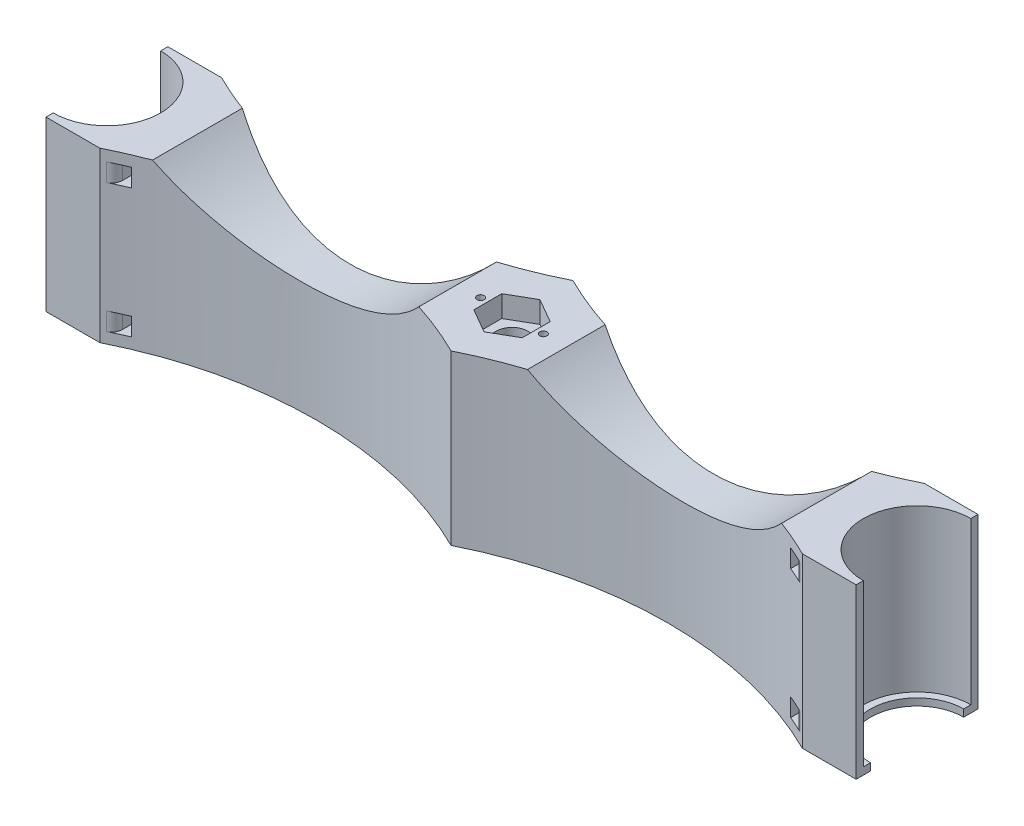
SolidWorks part; units mm, degrees
material "Copper"
ref_plane "Front Plane" through (0, 0, 0) normal (0, 0, 1) x (1, 0, 0)
ref_plane "Top Plane" through (0, 0, 0) normal (0, 1, 0) x (1, 0, 0)
ref_plane "Right Plane" through (0, 0, 0) normal (1, 0, 0) x (0, 0, -1)
sketch "Sketch1" plane through (0, 0, 0) normal (0, 1, 0) x (1, 0, 0)
  line L0 (0, 15) -> (0, 17)
  line L1 (0, -15) -> (0, -17)
  line L2 (113, 96.8217) -> (113, -79.4167) construction
  line L3 (0, 17) -> (15, 17)
  line L4 (226, -17) -> (211, -17)
  line L5 (226, 17) -> (211, 17)
  line L6 (0, -17) -> (15, -17)
  line L7 (226, -15) -> (226, -17)
  line L8 (226, 15) -> (226, 17)
  arc A0 (0, -15) -> (0, 15) centre (0, 0) ccw
  arc A1 (15, 17) -> (113, 17) centre (64, 115.4835) ccw
  arc A2 (15, -17) -> (113, -17) centre (64, -115.4835) cw
  arc A3 (211, -17) -> (113, -17) centre (162, -115.4835) ccw
  arc A4 (211, 17) -> (113, 17) centre (162, 115.4835) cw
  arc A5 (226, -15) -> (226, 15) centre (226, 0) cw
  dimension "D1" = 113
extrude "Boss-Extrude2" add sketch "Sketch1" along normal blind 47
sketch "Sketch2" plane through (0, 47, 0) normal (0, 1, 0) x (1, 0, 0)
  circle A0 centre (113, 0) radius 4.5
extrude "Cut-Extrude1" cut sketch "Sketch2" against normal through all
sketch "Sketch3" plane through (0, 47, 0) normal (0, 1, 0) x (1, 0, 0)
  line L1 (113, -7.7942) -> (119.75, -3.8971)
  line L2 (119.75, -3.8971) -> (119.75, 3.8971)
  line L3 (119.75, 3.8971) -> (113, 7.7942)
  line L4 (113, 7.7942) -> (106.25, 3.8971)
  line L5 (106.25, 3.8971) -> (106.25, -3.8971)
  line L6 (106.25, -3.8971) -> (113, -7.7942)
  circle A0 centre (113, 0) radius 6.75 construction
extrude "Cut-Extrude2" cut sketch "Sketch3" against normal blind 6
sketch "Sketch4" plane through (0, 47, 0) normal (0, 1, 0) x (1, 0, 0)
  line L0 (106.25, 3.8971) -> (106.25, -3.8971) construction
  line L1 (119.75, -3.8971) -> (119.75, 3.8971) construction
  circle A0 centre (104.25, 0) radius 1
  circle A1 centre (121.75, 0) radius 1
  dimension "D1" = 2
  dimension "D2" = 2
extrude "Cut-Extrude3" cut sketch "Sketch4" against normal blind 6
ref_plane "Plane1" through (0, 0, -17) normal (0, 0, -1) x (-1, 0, 0)
sketch "Sketch5" plane through (0, 0, -17) normal (0, 0, -1) x (-1, 0, 0)
  line L0 (-15, 47) -> (-113, 47) construction
  line L1 (-113, 47) -> (-113, 0) construction
  line L2 (-200.7496, 47) -> (-128.1535, 47)
  line L3 (-97.8465, 47) -> (-25.2504, 47)
  line L4 (-25.2504, 47) -> (-24.7481, 45.6215)
  arc A0 (-25.2504, 47) -> (-97.8465, 47) centre (-61.5485, 81.298) cw
  arc A1 (-200.7496, 47) -> (-128.1535, 47) centre (-164.4515, 81.298) ccw
extrude "Cut-Extrude4" cut sketch "Sketch5" against normal through all contours L2 A1 | A0 L3
sketch "Sketch6" plane through (0, 0, 0) normal (0, -1, 0) x (1, 0, 0)
  line L1 (120.5056, 0) -> (116.7528, 6.5)
  line L2 (116.7528, 6.5) -> (109.2472, 6.5)
  line L3 (109.2472, 6.5) -> (105.4944, 0)
  line L4 (105.4944, 0) -> (109.2472, -6.5)
  line L5 (109.2472, -6.5) -> (116.7528, -6.5)
  line L6 (116.7528, -6.5) -> (120.5056, 0)
  circle A0 centre (113, 0) radius 6.5 construction
extrude "Cut-Extrude5" cut sketch "Sketch6" against normal blind 6
sketch "Sketch7" plane through (0, 6, 0) normal (0, -1, 0) x (1, 0, 0)
  line L1 (120.5056, 0) -> (116.7528, 6.5)
  line L2 (116.7528, 6.5) -> (109.2472, 6.5)
  line L3 (109.2472, 6.5) -> (105.4944, 0)
  line L4 (105.4944, 0) -> (109.2472, -6.5)
  line L5 (109.2472, -6.5) -> (116.7528, -6.5)
  line L6 (116.7528, -6.5) -> (120.5056, 0)
  circle A0 centre (113, 0) radius 6.5 construction
extrude "Boss-Extrude3" add sketch "Sketch7" along normal blind 0.2
sketch "Sketch10" plane through (0, 0, 0) normal (0, -1, 0) x (1, 0, 0)
  line L0 (0, -13) -> (0, -15)
  line L1 (0, 13) -> (0, 15)
  line L3 (113, -17) -> (113, 17) construction
  line L4 (113, 17) -> (113, 64.6994) construction
  line L5 (226, 13) -> (226, 15)
  line L6 (226, -13) -> (226, -15)
  arc A0 (0, 13) -> (0, -13) centre (0, 0) cw
  arc A1 (0, -15) -> (0, 15) centre (0, 0) ccw
  arc A2 (226, -15) -> (226, 15) centre (226, 0) cw
  arc A3 (226, 13) -> (226, -13) centre (226, 0) ccw
extrude "Boss-Extrude4" add sketch "Sketch10" against normal blind 2 contours A2 L5 A3 L6 | L1 A0 L0 A1
sketch "Sketch11" plane through (0, 0, -17) normal (0, 0, -1) x (-1, 0, 0)
  line L0 (-15, 47) -> (-25.2504, 47) construction
  line L1 (-21.0454, 44) -> (-18, 44)
  line L2 (-21.0454, 44) -> (-21.0454, 39)
  line L3 (-21.0454, 39) -> (-18, 39)
  line L4 (-18, 44) -> (-18, 39)
  line L5 (0, 47) -> (0, 0) construction
  line L6 (-113, 23.5) -> (6.1803, 23.5) construction
  line L7 (-113, 47) -> (-113, 0) construction
  line L8 (-18, 3) -> (-18, 8)
  line L9 (-21.0454, 8) -> (-18, 8)
  line L10 (-21.0454, 3) -> (-21.0454, 8)
  line L11 (-21.0454, 3) -> (-18, 3)
  line L12 (-204.9546, 3) -> (-208, 3)
  line L13 (-204.9546, 3) -> (-204.9546, 8)
  line L14 (-204.9546, 8) -> (-208, 8)
  line L15 (-208, 3) -> (-208, 8)
  line L16 (-208, 44) -> (-208, 39)
  line L17 (-204.9546, 39) -> (-208, 39)
  line L18 (-204.9546, 44) -> (-204.9546, 39)
  line L19 (-204.9546, 44) -> (-208, 44)
  dimension "D1" = 3
  dimension "D2" = 18
extrude "Cut-Extrude6" cut sketch "Sketch11" against normal through all
fillet "Fillet1" radius 3 2 edges at (18, 5.5, -15.5635) (18, 41.5, -15.5635)
fillet "Fillet2" radius 3 6 edges at (208, 41.5, -15.5635) (208, 5.5, -15.5635) (208, 41.5, 15.5635) (208, 5.5, 15.5635) (18, 5.5, 15.5635) (18, 41.5, 15.5635)
